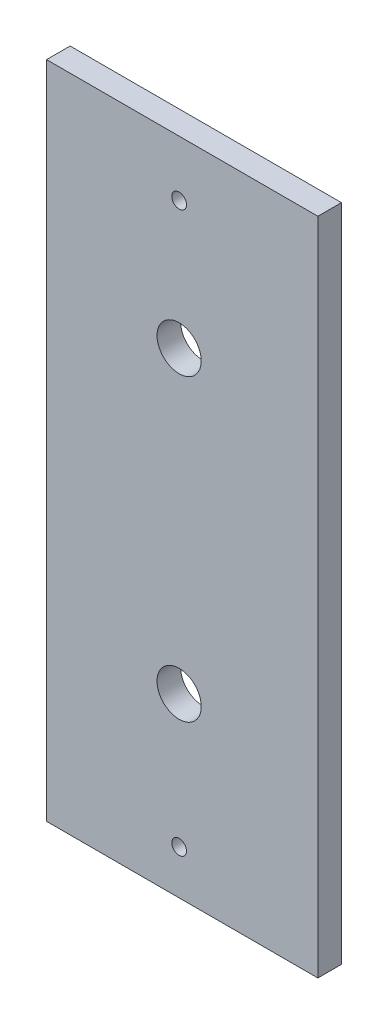
SolidWorks part; units mm, degrees
material "Epoxy, Unfilled"
ref_plane "Front Plane" through (0, 0, 0) normal (0, 0, 1) x (1, 0, 0)
ref_plane "Top Plane" through (0, 0, 0) normal (0, 1, 0) x (1, 0, 0)
ref_plane "Right Plane" through (0, 0, 0) normal (1, 0, 0) x (0, 0, -1)
sketch "Model" plane through (0, 0, 0) normal (0, 0, 1) x (1, 0, 0)
  line L0 (0, 0) -> (18.42, 0)
  line L1 (18.42, 0) -> (18.42, 44.79)
  line L2 (18.42, 44.79) -> (0, 44.79)
  line L3 (0, 44.79) -> (0, 0)
  line L4 (12.048, 13.016) -> (12.048, 14.54) construction
  line L5 (12.048, 14.54) -> (11.54, 15.048) construction
  line L6 (11.54, 8.952) -> (12.048, 9.46) construction
  line L7 (12.048, 9.46) -> (12.048, 10.984) construction
  line L8 (6.46, 15.048) -> (5.952, 14.54) construction
  line L9 (5.952, 14.54) -> (5.952, 13.016) construction
  line L10 (6.46, 8.952) -> (5.952, 9.46) construction
  line L11 (5.952, 9.46) -> (5.952, 10.984) construction
  line L12 (11.54, 8.952) -> (11.159, 8.952) construction
  line L13 (6.46, 8.952) -> (6.841, 8.952) construction
  line L14 (6.46, 15.048) -> (6.841, 15.048) construction
  line L15 (11.54, 15.048) -> (11.159, 15.048) construction
  line L16 (11.159, 15.048) -> (6.841, 15.048) construction
  line L17 (6.841, 8.952) -> (11.159, 8.952) construction
  line L18 (12.048, 12.998) -> (12.048, 10.984) construction
  line L19 (5.952, 13.028) -> (5.952, 10.984) construction
  line L20 (6.46, 13.27) -> (6.46, 12.508) construction
  line L21 (6.46, 11.492) -> (6.46, 10.73) construction
  line L22 (6.46, 12.508) -> (6.841, 11.619) construction
  line L116 (12.048, 33.336) -> (12.048, 34.86) construction
  line L117 (12.048, 34.86) -> (11.54, 35.368) construction
  line L118 (11.54, 29.272) -> (12.048, 29.78) construction
  line L119 (12.048, 29.78) -> (12.048, 31.304) construction
  line L120 (6.46, 35.368) -> (5.952, 34.86) construction
  line L121 (5.952, 34.86) -> (5.952, 33.336) construction
  line L122 (6.46, 29.272) -> (5.952, 29.78) construction
  line L123 (5.952, 29.78) -> (5.952, 31.304) construction
  line L126 (6.46, 35.368) -> (6.841, 35.368) construction
  line L127 (11.54, 35.368) -> (11.159, 35.368) construction
  line L128 (11.159, 35.368) -> (6.841, 35.368) construction
  line L129 (6.841, 29.272) -> (11.159, 29.272) construction
  line L130 (12.048, 33.318) -> (12.048, 31.304) construction
  line L131 (5.952, 33.348) -> (5.952, 31.304) construction
  line L132 (6.46, 33.59) -> (6.46, 32.828) construction
  line L133 (6.46, 31.812) -> (6.46, 31.05) construction
  line L134 (6.46, 32.828) -> (6.841, 31.939) construction
  circle A0 centre (5.7488, 14.2606) radius 0.9398 construction
  circle A1 centre (5.7488, 14.2606) radius 0.9398 construction
  circle A2 centre (12.2512, 14.2606) radius 0.9398 construction
  circle A3 centre (12.2512, 14.2606) radius 0.9398 construction
  circle A4 centre (5.7488, 9.7394) radius 0.9398 construction
  circle A5 centre (5.7488, 9.7394) radius 0.9398 construction
  circle A6 centre (12.2512, 9.7394) radius 0.9398 construction
  circle A7 centre (12.2512, 9.7394) radius 0.9398 construction
  circle A8 centre (5.7488, 34.5806) radius 0.9398 construction
  circle A9 centre (5.7488, 34.5806) radius 0.9398 construction
  circle A10 centre (12.2512, 34.5806) radius 0.9398 construction
  circle A11 centre (12.2512, 34.5806) radius 0.9398 construction
  circle A12 centre (5.7488, 30.0594) radius 0.9398 construction
  circle A13 centre (5.7488, 30.0594) radius 0.9398 construction
  circle A14 centre (12.2512, 30.0594) radius 0.9398 construction
  circle A15 centre (12.2512, 30.0594) radius 0.9398 construction
  circle A16 centre (9, 41) radius 0.5
  circle A17 centre (9, 32.32) radius 1.5
  circle A18 centre (9, 3) radius 0.5
  circle A19 centre (9, 12) radius 1.5
  circle A20 centre (9, 12) radius 1.778 construction
  circle A63 centre (9, 32.32) radius 1.778 construction
  point P546 (9, 12)
  point P547 (9, 32.32)
extrude "Boss-Extrude1" add sketch "Model" along normal blind 1.6
